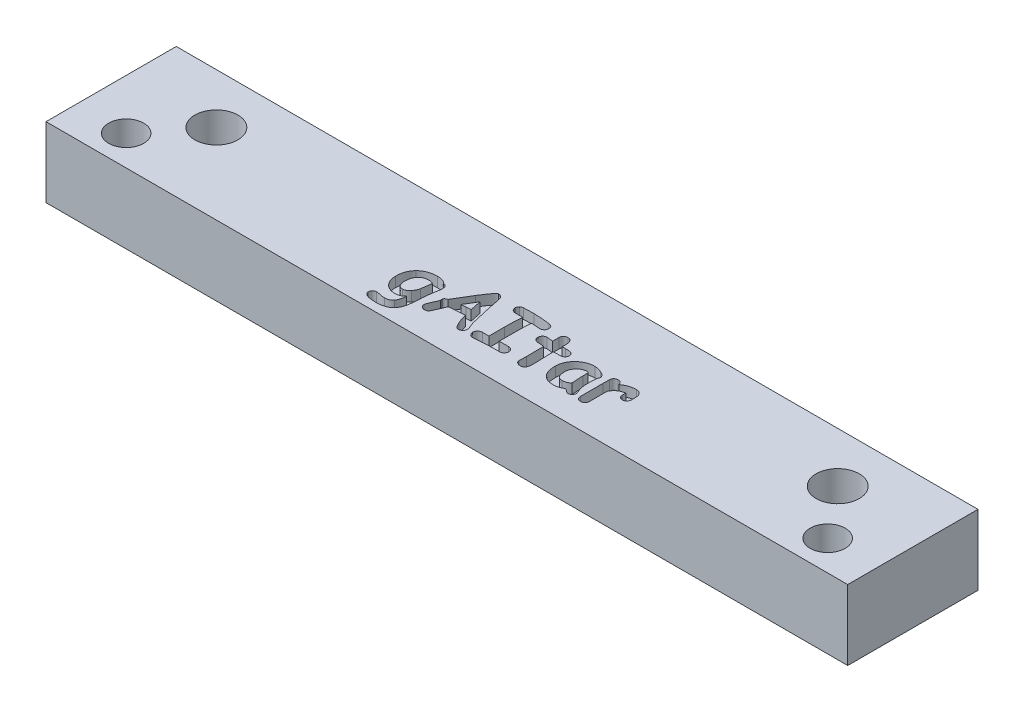
SolidWorks part; units mm, degrees
ref_plane "Front Plane" through (0, 0, 0) normal (0, 0, 1) x (1, 0, 0)
ref_plane "Top Plane" through (0, 0, 0) normal (0, 1, 0) x (1, 0, 0)
ref_plane "Right Plane" through (0, 0, 0) normal (1, 0, 0) x (0, 0, -1)
sketch "Sketch1" plane through (0, 0, 0) normal (0, 1, 0) x (1, 0, 0)
  line L0 (-5.2629, -24.2808) -> (74.7371, -24.2808)
  line L1 (74.7371, -24.2808) -> (74.7371, -37.2808)
  line L2 (-5.2629, -24.2808) -> (13.6704, -24.2808)
  line L3 (63.3564, -24.2808) -> (74.7371, -24.2808)
  line L4 (74.7371, -37.2808) -> (-5.2629, -37.2808)
  line L5 (-5.2629, -36.7808) -> (-5.2629, -37.2808)
  line L6 (-5.2629, -36.7808) -> (-5.2629, -24.2808)
  line L7 (-5.2629, -29.2808) -> (74.7371, -29.2808) construction
  line L8 (-0.2629, -24.2808) -> (-0.2629, -44.2808) construction
  line L9 (69.7371, -44.2808) -> (69.7371, -24.2808) construction
  line L11 (-5.2629, -36.7808) -> (74.7371, -36.7808) construction
  circle A0 centre (-0.2629, -34.2808) radius 1.75
  circle A1 centre (69.7371, -34.2808) radius 1.75
  circle A2 centre (3.7371, -29.2808) radius 2.15
  circle A3 centre (65.7371, -29.2808) radius 2.15
  dimension "D6" = 62
  dimension "D9" = 8
  dimension "D1" = 3
  dimension "D3" = 5
  dimension "D5" = 3
  dimension "D7" = 9
  dimension "D8" = 9
  dimension "D10" = 5
extrude "Boss-Extrude1" add sketch "Sketch1" against normal blind 7
sketch "Sketch2" plane through (0, 0, 0) normal (0, 1, 0) x (1, 0, 0)
  text T0 "<b>gAItar</b>" font "Comic Sans MS" height in points 18
extrude "Cut-Extrude1" cut sketch "Sketch2" against normal blind 1
